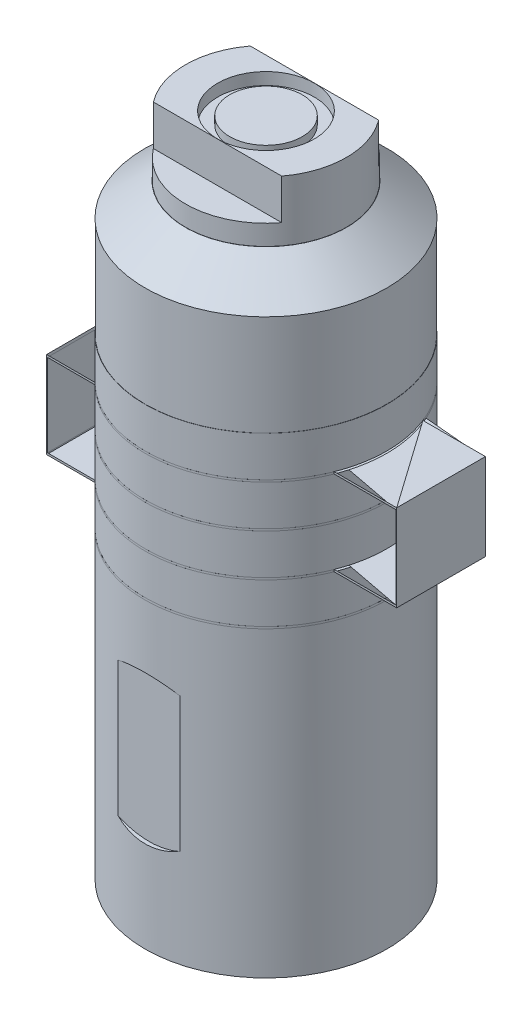
SolidWorks part; units mm, degrees
ref_plane "Front Plane" through (0, 0, 0) normal (0, 0, 1) x (1, 0, 0)
ref_plane "Top Plane" through (0, 0, 0) normal (0, 1, 0) x (1, 0, 0)
ref_plane "Right Plane" through (0, 0, 0) normal (1, 0, 0) x (0, 0, -1)
sketch "Sketch1" plane through (0, 0, 0) normal (0, 1, 0) x (1, 0, 0)
  circle A0 centre (0, 0) radius 30
  dimension "D1" = 60
extrude "Boss-Extrude1" add sketch "Sketch1" along normal blind 10
sketch "Sketch2" plane through (0, 0, 0) normal (0, -1, 0) x (1, 0, 0)
  circle A0 centre (0, 0) radius 15
  dimension "D1" = 30
extrude "Cut-Extrude1" cut sketch "Sketch2" against normal blind 10
sketch "Sketch7" plane through (0, 10, 0) normal (0, 1, 0) x (1, 0, 0)
  line L0 (0, -23.5) -> (-0.5, -23.5)
  line L1 (-0.5, -23.5) -> (-0.5, -22)
  line L2 (-0.5, -22) -> (-2, -22)
  line L3 (-2, -22) -> (-2, -21.5)
  line L4 (-2, -21.5) -> (-0.5, -21.5)
  line L5 (-0.5, -21.5) -> (-0.5, -20)
  line L6 (-0.5, -20) -> (0, -20)
  line L7 (0, -20) -> (0, -21.5)
  line L8 (0, -21.5) -> (1.5, -21.5)
  line L9 (1.5, -21.5) -> (1.5, -22)
  line L10 (1.5, -22) -> (0, -22)
  line L11 (0, -22) -> (0, -23.5)
  dimension "D1" = 1.5
  dimension "D2" = 1.5
  dimension "D3" = 0.5
  dimension "D4" = 0.5
  dimension "D5" = 1.5
  dimension "D6" = 1.5
  dimension "D7" = 0.5
  dimension "D8" = 1.5
  dimension "D9" = 20
extrude "Cut-Extrude4" cut sketch "Sketch7" against normal blind 0.01
sketch "Sketch8" plane through (0, 10, 0) normal (0, 1, 0) x (1, 0, 0)
  line L1 (27.9159, 11) -> (43.4159, 11)
  line L3 (27.9159, -11) -> (43.4159, -11)
  line L4 (43.4159, 11) -> (43.4159, -11)
  arc A0 (27.9159, 11) -> (27.9159, -11) centre (0, 0) ccw
  point P3 (30.005, 0)
  point P5 (-30.005, 0)
  dimension "D2" = 15.5
  dimension "D3" = 22
  dimension "D4" = 15.5
extrude "Boss-Extrude2" add sketch "Sketch8" along normal blind 0.5
sketch "Sketch9" plane through (0, 10.5, 0) normal (0, 1, 0) x (1, 0, 0)
  circle A0 centre (0, 0) radius 30
  dimension "D1" = 60
extrude "Boss-Extrude3" add sketch "Sketch9" along normal blind 10
sketch "Sketch10" plane through (0, 20.5, 0) normal (0, 1, 0) x (1, 0, 0)
  line L1 (-43.4159, 11) -> (-27.9159, 11)
  line L2 (-43.4159, 11) -> (-43.4159, -11)
  line L3 (-43.4159, -11) -> (-27.9159, -11)
  arc A0 (-27.9159, -11) -> (-27.9159, 11) centre (0, 0) ccw
  point P3 (-30.005, 0)
  dimension "D1" = 60.01
  dimension "D2" = 22
  dimension "D3" = 15.5
extrude "Boss-Extrude4" add sketch "Sketch10" along normal blind 0.5
pattern_linear "LPattern1" count 2 spacing 21 along (0, -1, 0) of "Boss-Extrude4"
sketch "Sketch11" plane through (0, 21, 0) normal (0, 1, 0) x (1, 0, 0)
  circle A0 centre (0, 0) radius 30
  dimension "D1" = 60
extrude "Boss-Extrude5" add sketch "Sketch11" along normal blind 10
pattern_linear "LPattern2" count 2 spacing 21 along (0, 1, 0) of "Boss-Extrude2"
sketch "Sketch12" plane through (0, 31.5, 0) normal (0, 1, 0) x (1, 0, 0)
  circle A0 centre (0, 0) radius 30
  dimension "D1" = 60
extrude "Boss-Extrude6" add sketch "Sketch12" along normal blind 10
sketch "Sketch13" plane through (0, 31, 0) normal (0, -1, 0) x (1, 0, 0)
  line L0 (43.4159, -11) -> (27.9159, -11) construction
  line L1 (43.4159, 11) -> (43.2159, 11)
  line L2 (43.4159, 11) -> (43.4159, -11)
  line L3 (43.4159, -11) -> (43.2159, -11)
  line L4 (43.2159, 11) -> (43.2159, -11)
  dimension "D1" = 0.2
extrude "Boss-Extrude7" add sketch "Sketch13" along normal blind 20.5
sketch "Sketch14" plane through (0, 20.5, 0) normal (0, -1, 0) x (1, 0, 0)
  line L0 (-43.4159, 11) -> (-27.9159, 11) construction
  line L1 (-43.4159, -11) -> (-43.2159, -11)
  line L2 (-43.4159, -11) -> (-43.4159, 11)
  line L3 (-43.4159, 11) -> (-43.2159, 11)
  line L4 (-43.2159, -11) -> (-43.2159, 11)
  dimension "D1" = 0.2
extrude "Boss-Extrude8" add sketch "Sketch14" along normal blind 20.5
sketch "Sketch15" plane through (0, -0.5, 0) normal (0, -1, 0) x (1, 0, 0)
  circle A0 centre (0, 0) radius 30
extrude "Boss-Extrude9" add sketch "Sketch15" along normal blind 75
sketch "Sketch16" plane through (0, -75.5, 0) normal (0, -1, 0) x (1, 0, 0)
  circle A0 centre (0, 0) radius 18
  dimension "D1" = 36
extrude "Cut-Extrude5" cut sketch "Sketch16" against normal blind 2
sketch "Sketch42" plane through (0, 41.5, 0) normal (0, 1, 0) x (1, 0, 0)
  circle A0 centre (0, 0) radius 29.95
  dimension "D1" = 59.9
extrude "Boss-Extrude10" add sketch "Sketch42" along normal blind 25
sketch "Sketch44" plane through (0, 66.5, 0) normal (0, 1, 0) x (1, 0, 0)
  point P0 (0, 0)
ref_plane "Plane2" through (0, 0, 0) normal (0, 0, 1) x (1, 0, 0)
sketch "Sketch45" plane through (0, 0, 0) normal (0, 0, 1) x (1, 0, 0)
  line L0 (0, 66.5) -> (30, 66.5)
  line L1 (30, 66.5) -> (20, 74.5)
  line L2 (20, 74.5) -> (0, 74.5)
  line L3 (0, 74.5) -> (0, 66.5)
  dimension "D1" = 8
  dimension "D2" = 20
  dimension "D3" = 270
revolve "Revolve1" add sketch "Sketch45" angle 360 about L3
sketch "Sketch46" plane through (0, 74.5, 0) normal (0, 1, 0) x (1, 0, 0)
  circle A0 centre (0, 0) radius 19.95
  dimension "D1" = 39.9
extrude "Boss-Extrude11" add sketch "Sketch46" along normal blind 15
sketch "Sketch47" plane through (0, 89.5, 0) normal (0, 1, 0) x (1, 0, 0)
  line L5 (-15.9228, 12.0195) -> (15.9228, 12.0195)
  line L7 (-15.9228, -12.0195) -> (15.9228, -12.0195)
  arc A2 (15.9228, 12.0195) -> (-15.9228, 12.0195) centre (0, 0) ccw
  arc A3 (-15.9228, -12.0195) -> (15.9228, -12.0195) centre (0, 0) ccw
extrude "Cut-Extrude8" cut sketch "Sketch47" against normal blind 10
sketch "Sketch48" plane through (0, 89.5, 0) normal (0, 1, 0) x (1, 0, 0)
  circle A0 centre (0, 0) radius 12
  dimension "D1" = 24
extrude "Cut-Extrude9" cut sketch "Sketch48" against normal blind 3
sketch "Sketch49" plane through (0, 86.5, 0) normal (0, 1, 0) x (1, 0, 0)
  circle A0 centre (0, 0) radius 9
  dimension "D1" = 18
extrude "Boss-Extrude12" add sketch "Sketch49" along normal blind 2
ref_plane "Plane3" through (0, 0, 30) normal (0, 0, 1) x (1, 0, 0)
sketch "Sketch50" plane through (0, 0, 30) normal (0, 0, 1) x (1, 0, 0)
  line L2 (-9.0749, -50.5) -> (-9.0749, -18.5)
  line L4 (9.0749, -50.5) -> (9.0749, -18.5)
  arc A0 (9.0749, -18.5) -> (-9.0749, -18.5) centre (0, -34.5) ccw
  arc A1 (-9.0749, -50.5) -> (9.0749, -50.5) centre (0, -34.5) ccw
  point P0 (0, -34.5)
  dimension "D2" = 32
extrude "Cut-Extrude10" cut sketch "Sketch50" against normal blind 1
mirror "Mirror1" about plane through (0, 0, 0) normal (0, 0, 1) of "Cut-Extrude10"
sketch "Sketch51" plane through (0, -73.5, 0) normal (0, -1, 0) x (1, 0, 0)
  circle A0 centre (0, 0) radius 10
hole_wizard "M20x1.5 Tapped Hole1" positions "3DSketch1" profile "Sketch52" tap size "M20x1.5" standard "GB"
sketch3d "3DSketch1"
  point P0 (0, -73.5, 0)
sketch "Sketch52" plane through (0, -73.5, 0) normal (1, 0, 0) x (0, 0, -1)
  line L0 (0, 0) -> (0, 40.058)
  line L1 (0, 40.058) -> (9.25, 34.5)
  line L2 (9.25, 34.5) -> (9.25, 0)
  line L5 (9.25, 0) -> (0, 0)
  line L10 (0, 40.058) -> (-9.25, 34.5) construction
  line L11 (0, -6.35) -> (0, 107.95) construction
  dimension "Tap Drill Dia." = 18.5
  dimension "Tap Drill Depth" = 34.5
  dimension "Drill Angle" = 118
cosmetic thread "Hole Thread1" parameters "D1"=30, "D2"=20
